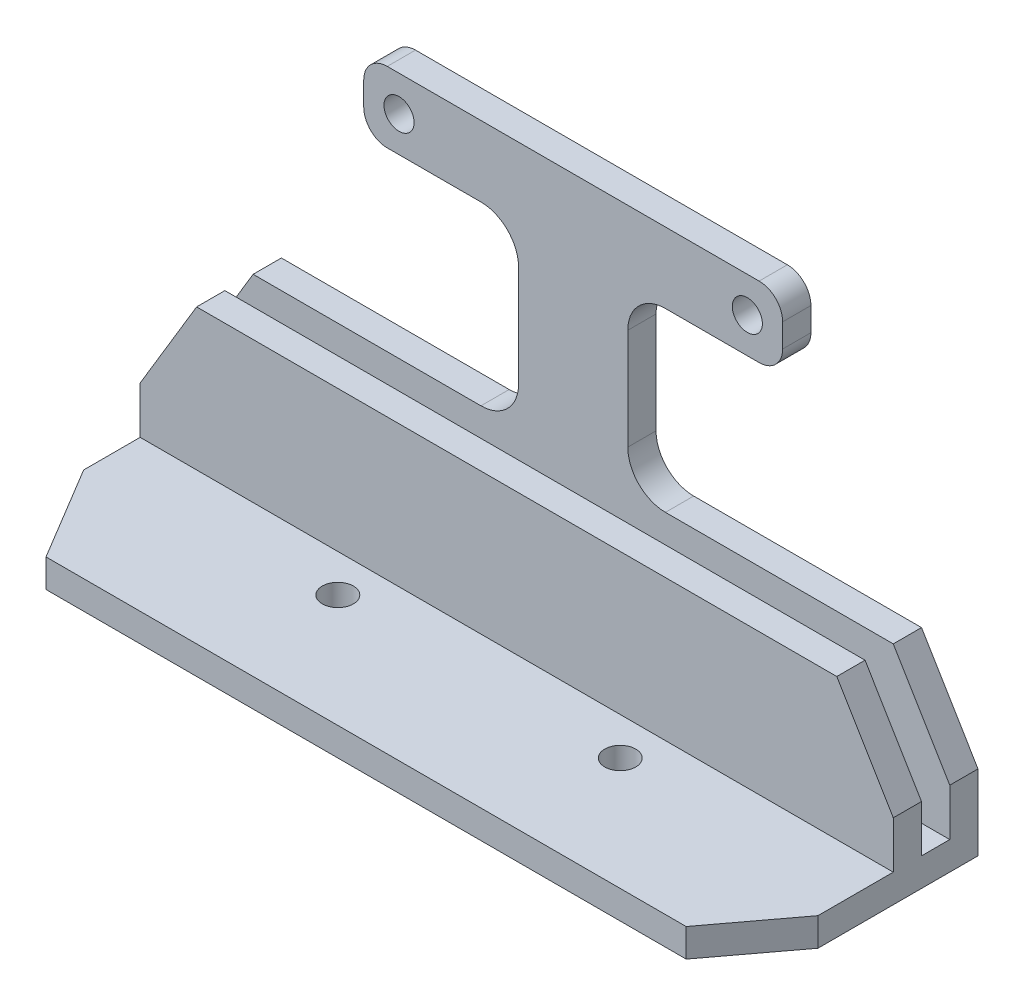
SolidWorks part; units mm, degrees
ref_plane "Ön Düzlem" through (0, 0, 0) normal (0, 0, 1) x (1, 0, 0)
ref_plane "Üst Düzlem" through (0, 0, 0) normal (0, 1, 0) x (1, 0, 0)
ref_plane "Sağ Düzlem" through (0, 0, 0) normal (1, 0, 0) x (0, 0, -1)
sketch "Sketch1" plane through (0, 0, 0) normal (0, 0, 1) x (1, 0, 0)
  line L0 (40, -2.5) -> (34, 7.5)
  line L1 (-34, 7.5) -> (-40, -2.5)
  line L2 (40, -7.5) -> (-40, -7.5)
  line L3 (40, -7.5) -> (40, -2.5)
  line L4 (34, 7.5) -> (-34, 7.5)
  line L5 (-40, -7.5) -> (-40, -2.5)
  line L6 (40, -7.5) -> (-40, 7.5) construction
  line L7 (40, 7.5) -> (-40, -7.5) construction
  dimension "D1" = 15
  dimension "D2" = 80
  dimension "D3" = 6
  dimension "D4" = 10
  dimension "D5" = 6
  dimension "D6" = 10
ref_plane "Plane1" through (0, -7.5, 0) normal (0, 1, 0) x (1, 0, 0)
sketch "Sketch2" plane through (0, -7.5, 0) normal (0, 1, 0) x (1, 0, 0)
  line L0 (0, 3) -> (0, 0) construction
  line L1 (-40, 0) -> (40, 0)
  line L2 (-40, 0) -> (-40, 3)
  line L3 (-40, 3) -> (40, 3)
  line L4 (40, 0) -> (40, 3)
  line L6 (40, -3) -> (-40, -3)
  line L7 (40, -3) -> (40, 6)
  line L8 (40, 6) -> (-40, 6)
  line L9 (-40, -3) -> (-40, 6)
  line L10 (40, -3) -> (-40, 6) construction
  line L11 (40, 6) -> (-40, -3) construction
  point P7 (0, 1.5)
  dimension "D1" = 80
  dimension "D2" = 3
  dimension "D3" = 9
  dimension "D4" = 80
ref_plane "Plane2" through (0, 0, -3) normal (0, 0, -1) x (-1, 0, 0)
sketch "Sketch3" plane through (0, 0, -3) normal (0, 0, -1) x (-1, 0, 0)
  line L0 (0, 30) -> (-18.5, 30) construction
  line L1 (40, -7.5) -> (-40, -7.5)
  line L2 (40, -7.5) -> (40, -2.5)
  line L3 (34, 7.5) -> (9.8, 7.5)
  line L4 (-40, -7.5) -> (-40, -2.5)
  line L5 (0, 30) -> (18.5, 30) construction
  line L6 (19.75, 26.25) -> (9.8, 26.25)
  line L7 (22.25, 28.75) -> (22.25, 31.25)
  line L8 (19.75, 33.75) -> (-19.75, 33.75)
  line L9 (-22.25, 28.75) -> (-22.25, 31.25)
  line L10 (22.25, 26.25) -> (-22.25, 33.75) construction
  line L11 (22.25, 33.75) -> (-22.25, 26.25) construction
  line L12 (-9.8, 7.5) -> (-34, 7.5)
  line L14 (-9.8, 26.25) -> (-19.75, 26.25)
  line L16 (-5.8, 22.25) -> (-5.8, 11.5)
  line L18 (5.8, 22.25) -> (5.8, 11.5)
  line L19 (-34, 7.5) -> (-40, -2.5)
  line L20 (40, -2.5) -> (34, 7.5)
  arc A0 (-22.25, 31.25) -> (-19.75, 33.75) centre (-19.75, 31.25) cw
  arc A1 (-22.25, 28.75) -> (-19.75, 26.25) centre (-19.75, 28.75) ccw
  arc A2 (19.75, 33.75) -> (22.25, 31.25) centre (19.75, 31.25) cw
  arc A3 (22.25, 28.75) -> (19.75, 26.25) centre (19.75, 28.75) cw
  arc A4 (5.8, 22.25) -> (9.8, 26.25) centre (9.8, 22.25) cw
  arc A5 (-5.8, 22.25) -> (-9.8, 26.25) centre (-9.8, 22.25) ccw
  circle A6 centre (-18.5, 30) radius 1.6
  circle A7 centre (18.5, 30) radius 1.6
  arc A8 (5.8, 11.5) -> (9.8, 7.5) centre (9.8, 11.5) ccw
  arc A9 (-5.8, 11.5) -> (-9.8, 7.5) centre (-9.8, 11.5) cw
  point P1 (-40, 7.5)
  point P2 (40, 7.5)
  point P5 (0, 30)
  point P30 (-5.8, 26.25)
  point P41 (-40, 7.5)
  dimension "D5" = 2.5
  dimension "D6" = 2.5
  dimension "D7" = 2.5
  dimension "D8" = 4
  dimension "D9" = 4
  dimension "D10" = 4
  dimension "D11" = 4
  dimension "D1" = 80
  dimension "D2" = 15
  dimension "D3" = 44.5
  dimension "D4" = 7.5
  dimension "D12" = 6
  dimension "D13" = 10
  dimension "D14" = 6
  dimension "D15" = 10
extrude "Boss-Extrude1" add sketch "Sketch1" along normal blind 3
extrude "Boss-Extrude2" add sketch "Sketch3" along normal blind 3 separate body
extrude "Boss-Extrude3" add sketch "Sketch2" against normal blind 3 contours L9 L3 L7 L8 | L1 L4 L3 L2 | L9 L6 L7 L1
sketch "Sketch5" plane through (0, 0, 3) normal (0, 0, 1) x (1, 0, 0)
sketch "Sketch6" plane through (0, 0, -6) normal (0, 0, -1) x (-1, 0, 0)
sketch "Sketch8" plane through (0, 0, 3) normal (0, 0, 1) x (1, 0, 0)
  line L0 (40, -10.5) -> (40, -2.5) construction
  line L1 (-40, -10.5) -> (40, -10.5)
  line L2 (-40, -10.5) -> (-40, -7.5)
  line L3 (-40, -7.5) -> (40, -7.5)
  line L4 (40, -10.5) -> (40, -7.5)
  dimension "D1" = 3
extrude "Boss-Extrude6" add sketch "Sketch8" along normal blind 16
sketch "Sketch21" plane through (0, -7.5, 0) normal (0, 1, 0) x (1, 0, 0)
  line L0 (0, -7) -> (-15, -7) construction
  line L6 (0, -7) -> (15, -7) construction
  circle A0 centre (-15, -7) radius 1.65
  circle A1 centre (15, -7) radius 1.65
extrude "Cut-Extrude1" cut sketch "Sketch21" against normal through all
sketch "Sketch24" plane through (0, -7.5, 0) normal (0, 1, 0) x (1, 0, 0)
  line L0 (-40, -19) -> (-40, -9)
  line L1 (-40, -19) -> (-40, -3) construction
  line L2 (-40, -19) -> (-34, -19)
  line L3 (40, -19) -> (-40, -19) construction
  line L4 (-34, -19) -> (-40, -9)
  line L5 (40, -19) -> (34, -19)
  line L6 (40, -19) -> (40, -11)
  line L7 (40, -19) -> (40, -3) construction
  line L8 (40, -11) -> (34, -19)
extrude "Cut-Extrude2" cut sketch "Sketch24" against normal through all
